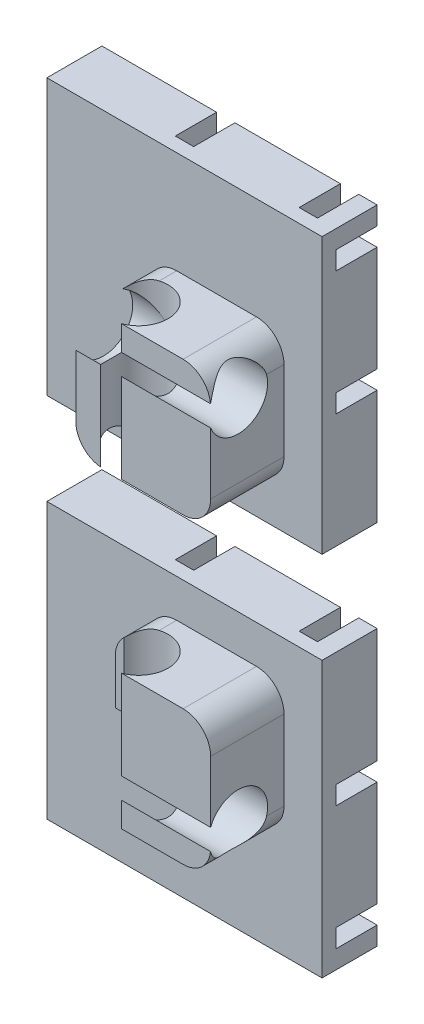
SolidWorks part; units mm, degrees
ref_plane "Front Plane" through (0, 0, 0) normal (0, 0, 1) x (1, 0, 0)
ref_plane "Top Plane" through (0, 0, 0) normal (0, 1, 0) x (1, 0, 0)
ref_plane "Right Plane" through (0, 0, 0) normal (1, 0, 0) x (0, 0, -1)
sketch "Sketch1" plane through (0, 0, 0) normal (0, 0, 1) x (1, 0, 0)
  line L1 (0, 0) -> (30, 0)
  line L2 (0, 0) -> (0, 30)
  line L3 (0, 30) -> (30, 30)
  line L4 (30, 0) -> (30, 30)
  dimension "D1" = 30
  dimension "D2" = 30
extrude "cover" add sketch "Sketch1" along normal blind 6
sketch "Sketch2" plane through (0, 0, 6) normal (0, 0, 1) x (1, 0, 0)
  line L0 (30, 30) -> (0, 30) construction
  line L1 (11.15, 25.85) -> (25.85, 25.85)
  line L2 (11.15, 25.85) -> (11.15, 11.15)
  line L3 (11.15, 11.15) -> (25.85, 11.15)
  line L4 (25.85, 25.85) -> (25.85, 11.15)
  line L6 (0, 0) -> (30, 0) construction
  line L7 (30, 0) -> (30, 30) construction
  line L8 (0, 30) -> (0, 0) construction
  dimension "D1" = 4.15
  dimension "D3" = 11.15
  dimension "D2" = 4.15
  dimension "D4" = 11.15
extrude "plug" add sketch "Sketch2" along normal blind 8
sketch "Sketch3" plane through (0, 0, 0) normal (0, 0, -1) x (-1, 0, 0)
  line L8 (0, 0) -> (-30, 0) construction
  line L10 (0, 2) -> (-30, 2)
  line L23 (0, 2) -> (0, 4)
  line L28 (0, 4) -> (-30, 4)
  line L29 (-30, 2) -> (-30, 4)
  line L34 (-30, 0) -> (-30, 30) construction
  line L40 (0, 15.5) -> (0, 17.5)
  line L41 (0, 15.5) -> (-30, 15.5)
  line L42 (-30, 15.5) -> (-30, 17.5)
  line L43 (0, 17.5) -> (-30, 17.5)
  line L58 (0, 30) -> (0, 0) construction
  line L59 (0, 56) -> (0, 58) [skipped]
  line L60 (0, 58) -> (-30, 58) [skipped]
  line L61 (-30, 56) -> (-30, 58) [skipped]
  line L62 (0, 56) -> (-30, 56) [skipped]
  line L63 (0, 42.5) -> (0, 44.5) [skipped]
  line L64 (0, 44.5) -> (-30, 44.5) [skipped]
  line L65 (-30, 42.5) -> (-30, 44.5) [skipped]
  line L66 (0, 42.5) -> (-30, 42.5) [skipped]
  line L67 (0, 29) -> (0, 31) [skipped]
  line L68 (0, 31) -> (-30, 31) [skipped]
  line L69 (-30, 29) -> (-30, 31) [skipped]
  line L70 (0, 29) -> (-30, 29) [skipped]
  dimension "D1" = 2
  dimension "D2" = 2
  dimension "D5" = 5
extrude "Cut-Extrude1" cut sketch "Sketch3" against normal blind 4.5
fillet "Fillet1" radius 3 4 edges at (11.15, 11.15, 10) (25.85, 11.15, 10) (25.85, 25.85, 10) (11.15, 25.85, 10)
fillet "Fillet2" [suppressed] radius 0.5
ref_plane "Plane1" through (0, 35, 0) normal (0, 1, 0) x (1, 0, 0)
sketch "Sketch7" plane through (0, 0, 0) normal (0, 0, -1) x (-1, 0, 0)
  line L0 (0, 0) -> (-30, 0) construction
  line L1 (-28, 0) -> (-26, 0)
  line L2 (-28, 0) -> (-28, 30)
  line L3 (-28, 30) -> (-26, 30)
  line L4 (-26, 0) -> (-26, 30)
  line L6 (-30, 4) -> (-30, 15.5) construction
  line L7 (-14.5, 0) -> (-14.5, 30)
  line L8 (-14.5, 0) -> (-12.5, 0)
  line L9 (-12.5, 0) -> (-12.5, 30)
  line L10 (-14.5, 30) -> (-12.5, 30)
  line L15 (-1, 0) -> (-1, 30) [skipped]
  line L16 (-1, 30) -> (1, 30) [skipped]
  line L17 (1, 0) -> (1, 30) [skipped]
  line L18 (-1, 0) -> (1, 0) [skipped]
  line L19 (-30, 30) -> (0, 30) construction
  dimension "D1" = 2
  dimension "D2" = 2
  dimension "D3" = 3
extrude "Cut-Extrude5" cut sketch "Sketch7" against normal up to surface (4.5 mm away) up to face at (15, 3, 4.5)
ref_plane "Plane2" through (0, 0, 14) normal (0, 0, 1) x (1, 0, 0)
sketch "Sketch10" plane through (0, 0, 0) normal (0, -1, 0) x (1, 0, 0)
  line L0 (0, 6) -> (30, 6) construction
  circle A0 centre (15, 11) radius 3.21
  point P4 (0, 0)
  point P5 (15, 6)
  dimension "D1" = 6.42
  dimension "D2" = 5
extrude "Cut-Extrude8" cut sketch "Sketch10" against normal up to surface (25.85 mm away) contours A0 up to face at (18.5, 25.85, 10)
sketch "Sketch8" plane through (30, 0, 0) normal (1, 0, 0) x (0, 0, -1)
  line L1 (-6, 0) -> (-6, 30) construction
  circle A0 centre (-11, 15) radius 3.21
  point P2 (-9.8997, 13.5814)
  point P5 (0, 0)
  point P6 (-6, 15)
  dimension "D2" = 6.42
  dimension "D1" = 5
extrude "Cut-Extrude6" cut sketch "Sketch8" against normal up to surface (18.85 mm away) up to face at (11.15, 18.5, 10)
delete or keep bodies "Body-Delete/Keep 1" type delete bodies bodies 117
sketch "Sketch11" plane through (0, 0, 0) normal (0, 0, -1) x (-1, 0, 0)
  circle A0 centre (-1.0235, 0.9575) radius 0.4
  point P2 (-0.9928, 0.8801)
  point P3 (-1.0235, 0.9575)
  dimension "D1" = 0.8
extrude "Cut-Extrude9" cut sketch "Sketch11" against normal blind 0.3
mirror "Mirror3" about plane through (0, 35, 0) normal (0, 1, 0) of bodies 118 109
sketch "Sketch12" plane through (11.15, 0, 0) normal (-1, 0, 0) x (0, 0, 1)
  line L1 (9.6894, 14.6344) -> (15.4763, 14.6344)
  line L2 (9.6894, 14.6344) -> (9.6894, 27.7012)
  line L3 (9.6894, 27.7012) -> (15.4763, 27.7012)
  line L4 (15.4763, 14.6344) -> (15.4763, 27.7012)
extrude "Cut-Extrude10" cut sketch "Sketch12" against normal up to vertex (1.35 mm away)
equation "\"cubeCham\" = 0.7mm"
equation "\"D1@Sketch1\"=\"cleatSpacing\""
equation "\"D2@Sketch1\"=\"cleatSpacing\""
equation "\"D1@cover\"=3mm"
equation "\"D1@Sketch2\" = \"wall2\""
equation "\"D3@Sketch2\" = \"cleatLen\" + \"wall2\""
equation "\"D1@plug\"=8mm"
equation "\"cleatShaftLen\" = 3"
equation "\"cleatHeadLen\" = 4mm"
equation "\"cleatHeadGirth\" = 12mm"
equation "\"cleatShaftGirth\" = 8mm"
equation "\"cleatTolOffset\" = 0.4mm"
equation "\"cleatCham\" = 1mm"
equation "\"cleatSpacing\" = 30mm"
equation "\"cleatTriangleAngle\" = 25deg"
equation "\"cleatMinimumTriangleAngle\" = 12deg"
equation "\"nCleats\" = 2"
equation "\"threadID\" = 8.3mm"
equation "\"threadPitch\" = 2mm"
equation "\"threadOD\" = 10.7mm"
equation "\"threadMaleOD\" = 10.0mm"
equation "\"cleatFemShaftLen\" = \"cleatShaftLen\" - \"cleatTolOffset\""
equation "\"cleatFemHeadLen\" = \"cleatHeadLen\" + \"cleatTolOffset\" * 1.25"
equation "\"cleatFemHeadGirth\" = \"cleatHeadGirth\" + \"cleatTolOffset\""
equation "\"cleatFemShaftGirth\" = \"cleatShaftGirth\" + \"cleatTolOffset\""
equation "\"lip\" = 2mm"
equation "\"cubeCutoutPadding\" = 3mm"
equation "\"wall\" = 3mm"
equation "\"wall2\" = 4.15mm"
equation "\"cleatLen\" = \"cleatShaftLen\" + \"cleatHeadLen\""
equation "\"coverThickness\" = 6mm"
equation "\"plugDepth\" = 8mm"
equation "\"bottomChamOffset\" = 1.8mm"
equation "\"maleHelperAngle\" = 45deg"
equation "\"maleHelperAngle2\" = 35deg"
equation "\"stFactor\" = 0.6"
equation "\"stID\" = \"threadID\" * \"stFactor\""
equation "\"stOD\" = \"threadOD\" * \"stFactor\""
equation "\"stPitch\" = \"threadPitch\" * \"stFactor\""
equation "\"stProtrusion\" = (\"stOD\" - \"stID\") / 2"
equation "\"stMaleOD\" = \"threadMaleOD\" * \"stFactor\""
equation "\"stHexDiam\" = 2.5mm"
equation "\"stHexPad\" = 0.08mm"
equation "\"stSocketHeadProtrusion\" = 0.65mm"
equation "\"stSocketHeadDiam\" = \"stOD\" + \"stSocketHeadProtrusion\""
equation "\"stSocketHeadLen\" = 1.2mm"
equation "\"stSocketHeadLenPad\" = 0.1mm"
equation "\"stSocketHeadCounterboreDepth\" = \"stSocketHeadLen\" + \"stSocketHeadLenPad\""
equation "\"stDriverDepth\" = 2mm"
equation "\"stNutODPad\" = 3mm"
equation "\"stNutDiam\" = \"stOD\" + \"stNutODPad\""
equation "\"stNutHeight\" = 3mm"
equation "\"stNutCham\" = 0.4mm"
equation "\"temp\" = 0"
equation "\"plugCornerFill\" = 3mm"
equation "\"D1@Fillet1\"=\"plugCornerFill\""
equation "\"D4@Sketch2\"=\"cleatLen\"+\"wall2\""
equation "\"D2@Sketch2\"=\"wall2\""
equation "\"cleatTolOffsetLoose\" = 0.6mm"
equation "\"cleatFemLen\" = \"cleatFemShaftLen\" + \"cleatFemHeadLen\""
equation "\"cleatFemLooseShaftLen\" = \"cleatShaftLen\" - \"cleatTolOffsetLoose\""
equation "\"cleatFemLooseHeadLen\" = \"cleatHeadLen\" + \"cleatTolOffsetLoose\" * 1.25"
equation "\"cleatFemLooseHeadGirth\" = \"cleatHeadGirth\" + \"cleatTolOffsetLoose\""
equation "\"cleatFemLooseShaftGirth\" = \"cleatShaftGirth\" + \"cleatTolOffsetLoose\""
equation "\"cleatFemLooseLen\" = \"cleatFemShaftLen\" + \"cleatFemHeadLen\""
equation "\"fsg\" = \"cleatFemShaftGirth\""
equation "\"fsl\" = \"cleatFemShaftLen\""
equation "\"fhg\" = \"cleatFemHeadGirth\""
equation "\"fhl\" = \"cleatFemHeadLen\""
equation "\"msg\" = \"cleatShaftGirth\""
equation "\"msl\" = \"cleatShaftLen\""
equation "\"mhg\" = \"cleatHeadGirth\""
equation "\"mhl\" = \"cleatHeadLen\""
equation "\"threadProtrusion\" = (\"threadOD\" - \"threadID\") / 2"
equation "\"threadMaleID\" = \"threadMaleOD\" - \"threadProtrusion\" * 2"
equation "\"threadMaleSocketDiam\" = 15.0mm"
equation "\"threadMaleHex\" = 6mm"
equation "\"stMaleID\" = \"threadMaleID\" * \"stFactor\""
equation "\"stFlatHeadDiamMale\" = 9.4mm"
equation "\"stFlatHeadDiamFemale\" = 9.6mm"
equation "\"stFlatHeadChamAngle\" = 45deg"
equation "\"stFlatHeadAxialLenMale\" = 1.7mm"
equation "\"stFlatHeadAxialLenFem\" = 1.9mm"
equation "\"cubeCutoutFem\" = \"cleatSpacing\" - \"cleatLen\" - 2*\"wall2\""
equation "\"cutoutDepth\" = 4.5mm"
equation "\"cutoutWidth\" = 2mm"
equation "\"cutoutSpacing\" = 13.5mm"
equation "\"D2@Sketch8\"=\"stOD\""
equation "\"D1@Sketch10\"=\"stOD\""
